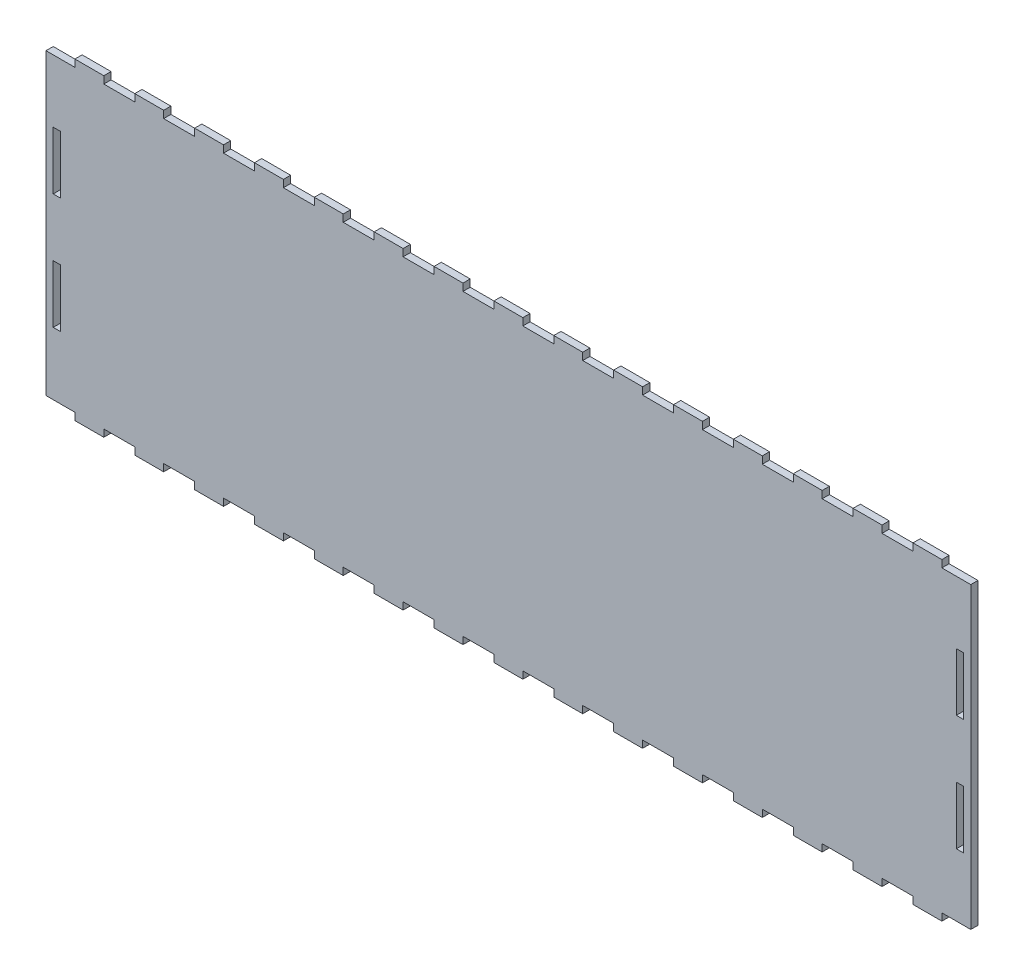
SolidWorks part; units mm, degrees
ref_plane "Front Plane" through (0, 0, 0) normal (0, 0, 1) x (1, 0, 0)
ref_plane "Top Plane" through (0, 0, 0) normal (0, 1, 0) x (1, 0, 0)
ref_plane "Right Plane" through (0, 0, 0) normal (1, 0, 0) x (0, 0, -1)
sketch "Sketch1" plane through (0, 0, 0) normal (0, 0, 1) x (1, 0, 0)
  line L8 (6.35, 78.3336) -> (6.35, 103.7336)
  line L9 (3.175, 78.3336) -> (6.35, 78.3336)
  line L10 (3.175, 103.7336) -> (3.175, 78.3336)
  line L11 (6.35, 103.7336) -> (3.175, 103.7336)
  line L16 (6.35, 27.5336) -> (6.35, 52.9336)
  line L17 (3.175, 27.5336) -> (6.35, 27.5336)
  line L18 (3.175, 52.9336) -> (3.175, 27.5336)
  line L19 (6.35, 52.9336) -> (3.175, 52.9336)
  line L24 (400.05, 103.7336) -> (400.05, 78.3336)
  line L25 (403.225, 103.7336) -> (400.05, 103.7336)
  line L26 (403.225, 78.3336) -> (403.225, 103.7336)
  line L27 (400.05, 78.3336) -> (403.225, 78.3336)
  line L32 (400.05, 52.9336) -> (400.05, 27.5336)
  line L33 (403.225, 52.9336) -> (400.05, 52.9336)
  line L34 (403.225, 27.5336) -> (403.225, 52.9336)
  line L35 (400.05, 27.5336) -> (403.225, 27.5336)
  line L248 (406.4, 0) -> (406.4, 131.2672)
  line L249 (406.4, 131.2672) -> (393.7, 131.2672)
  line L250 (393.7, 131.2672) -> (393.7, 134.4422)
  line L251 (393.7, 134.4422) -> (381, 134.4422)
  line L252 (381, 134.4422) -> (381, 131.2672)
  line L253 (381, 131.2672) -> (367.3929, 131.2672)
  line L254 (367.3929, 131.2672) -> (367.3929, 134.4422)
  line L255 (367.3929, 134.4422) -> (354.6929, 134.4422)
  line L256 (354.6929, 134.4422) -> (354.6929, 131.2672)
  line L257 (354.6929, 131.2672) -> (341.0857, 131.2672)
  line L258 (341.0857, 131.2672) -> (341.0857, 134.4422)
  line L259 (341.0857, 134.4422) -> (328.3857, 134.4422)
  line L260 (328.3857, 134.4422) -> (328.3857, 131.2672)
  line L261 (328.3857, 131.2672) -> (314.7786, 131.2672)
  line L262 (314.7786, 131.2672) -> (314.7786, 134.4422)
  line L263 (314.7786, 134.4422) -> (302.0786, 134.4422)
  line L264 (302.0786, 134.4422) -> (302.0786, 131.2672)
  line L265 (302.0786, 131.2672) -> (288.4714, 131.2672)
  line L266 (288.4714, 131.2672) -> (288.4714, 134.4422)
  line L267 (288.4714, 134.4422) -> (275.7714, 134.4422)
  line L268 (275.7714, 134.4422) -> (275.7714, 131.2672)
  line L269 (275.7714, 131.2672) -> (262.1643, 131.2672)
  line L270 (262.1643, 131.2672) -> (262.1643, 134.4422)
  line L271 (262.1643, 134.4422) -> (249.4643, 134.4422)
  line L272 (249.4643, 134.4422) -> (249.4643, 131.2672)
  line L273 (249.4643, 131.2672) -> (235.8571, 131.2672)
  line L274 (235.8571, 131.2672) -> (235.8571, 134.4422)
  line L275 (235.8571, 134.4422) -> (223.1571, 134.4422)
  line L276 (223.1571, 134.4422) -> (223.1571, 131.2672)
  line L277 (223.1571, 131.2672) -> (209.55, 131.2672)
  line L278 (209.55, 131.2672) -> (209.55, 134.4422)
  line L279 (209.55, 134.4422) -> (196.85, 134.4422)
  line L280 (196.85, 134.4422) -> (196.85, 131.2672)
  line L281 (196.85, 131.2672) -> (183.2429, 131.2672)
  line L282 (183.2429, 131.2672) -> (183.2429, 134.4422)
  line L283 (183.2429, 134.4422) -> (170.5429, 134.4422)
  line L284 (170.5429, 134.4422) -> (170.5429, 131.2672)
  line L285 (170.5429, 131.2672) -> (156.9357, 131.2672)
  line L286 (156.9357, 131.2672) -> (156.9357, 134.4422)
  line L287 (156.9357, 134.4422) -> (144.2357, 134.4422)
  line L288 (144.2357, 134.4422) -> (144.2357, 131.2672)
  line L289 (144.2357, 131.2672) -> (130.6286, 131.2672)
  line L290 (130.6286, 131.2672) -> (130.6286, 134.4422)
  line L291 (130.6286, 134.4422) -> (117.9286, 134.4422)
  line L292 (117.9286, 134.4422) -> (117.9286, 131.2672)
  line L293 (117.9286, 131.2672) -> (104.3214, 131.2672)
  line L294 (104.3214, 131.2672) -> (104.3214, 134.4422)
  line L295 (104.3214, 134.4422) -> (91.6214, 134.4422)
  line L296 (91.6214, 134.4422) -> (91.6214, 131.2672)
  line L297 (91.6214, 131.2672) -> (78.0143, 131.2672)
  line L298 (78.0143, 131.2672) -> (78.0143, 134.4422)
  line L299 (78.0143, 134.4422) -> (65.3143, 134.4422)
  line L300 (65.3143, 134.4422) -> (65.3143, 131.2672)
  line L301 (65.3143, 131.2672) -> (51.7071, 131.2672)
  line L302 (51.7071, 131.2672) -> (51.7071, 134.4422)
  line L303 (51.7071, 134.4422) -> (39.0071, 134.4422)
  line L304 (39.0071, 134.4422) -> (39.0071, 131.2672)
  line L305 (39.0071, 131.2672) -> (25.4, 131.2672)
  line L306 (25.4, 131.2672) -> (25.4, 134.4422)
  line L307 (25.4, 134.4422) -> (12.7, 134.4422)
  line L308 (12.7, 134.4422) -> (12.7, 131.2672)
  line L309 (12.7, 131.2672) -> (0, 131.2672)
  line L310 (0, 131.2672) -> (0, 0)
  line L311 (0, 0) -> (12.7, 0)
  line L312 (12.7, 0) -> (12.7, -3.175)
  line L313 (12.7, -3.175) -> (25.4, -3.175)
  line L314 (25.4, -3.175) -> (25.4, 0)
  line L315 (25.4, 0) -> (39.0071, 0)
  line L316 (39.0071, 0) -> (39.0071, -3.175)
  line L317 (39.0071, -3.175) -> (51.7071, -3.175)
  line L318 (51.7071, -3.175) -> (51.7071, 0)
  line L319 (51.7071, 0) -> (65.3143, 0)
  line L320 (65.3143, 0) -> (65.3143, -3.175)
  line L321 (65.3143, -3.175) -> (78.0143, -3.175)
  line L322 (78.0143, -3.175) -> (78.0143, 0)
  line L323 (78.0143, 0) -> (91.6214, 0)
  line L324 (91.6214, 0) -> (91.6214, -3.175)
  line L325 (91.6214, -3.175) -> (104.3214, -3.175)
  line L326 (104.3214, -3.175) -> (104.3214, 0)
  line L327 (104.3214, 0) -> (117.9286, 0)
  line L328 (117.9286, 0) -> (117.9286, -3.175)
  line L329 (117.9286, -3.175) -> (130.6286, -3.175)
  line L330 (130.6286, -3.175) -> (130.6286, 0)
  line L331 (130.6286, 0) -> (144.2357, 0)
  line L332 (144.2357, 0) -> (144.2357, -3.175)
  line L333 (144.2357, -3.175) -> (156.9357, -3.175)
  line L334 (156.9357, -3.175) -> (156.9357, 0)
  line L335 (156.9357, 0) -> (170.5429, 0)
  line L336 (170.5429, 0) -> (170.5429, -3.175)
  line L337 (170.5429, -3.175) -> (183.2429, -3.175)
  line L338 (183.2429, -3.175) -> (183.2429, 0)
  line L339 (183.2429, 0) -> (196.85, 0)
  line L340 (196.85, 0) -> (196.85, -3.175)
  line L341 (196.85, -3.175) -> (209.55, -3.175)
  line L342 (209.55, -3.175) -> (209.55, 0)
  line L343 (209.55, 0) -> (223.1571, 0)
  line L344 (223.1571, 0) -> (223.1571, -3.175)
  line L345 (223.1571, -3.175) -> (235.8571, -3.175)
  line L346 (235.8571, -3.175) -> (235.8571, 0)
  line L347 (235.8571, 0) -> (249.4643, 0)
  line L348 (249.4643, 0) -> (249.4643, -3.175)
  line L349 (249.4643, -3.175) -> (262.1643, -3.175)
  line L350 (262.1643, -3.175) -> (262.1643, 0)
  line L351 (262.1643, 0) -> (275.7714, 0)
  line L352 (275.7714, 0) -> (275.7714, -3.175)
  line L353 (275.7714, -3.175) -> (288.4714, -3.175)
  line L354 (288.4714, -3.175) -> (288.4714, 0)
  line L355 (288.4714, 0) -> (302.0786, 0)
  line L356 (302.0786, 0) -> (302.0786, -3.175)
  line L357 (302.0786, -3.175) -> (314.7786, -3.175)
  line L358 (314.7786, -3.175) -> (314.7786, 0)
  line L359 (314.7786, 0) -> (328.3857, 0)
  line L360 (328.3857, 0) -> (328.3857, -3.175)
  line L361 (328.3857, -3.175) -> (341.0857, -3.175)
  line L362 (341.0857, -3.175) -> (341.0857, 0)
  line L363 (341.0857, 0) -> (354.6929, 0)
  line L364 (354.6929, 0) -> (354.6929, -3.175)
  line L365 (354.6929, -3.175) -> (367.3929, -3.175)
  line L366 (367.3929, -3.175) -> (367.3929, 0)
  line L367 (367.3929, 0) -> (381, 0)
  line L368 (381, 0) -> (381, -3.175)
  line L369 (381, -3.175) -> (393.7, -3.175)
  line L370 (393.7, -3.175) -> (393.7, 0)
  line L371 (393.7, 0) -> (406.4, 0)
extrude "Boss-Extrude1" add sketch "Sketch1" along normal blind 3.175
